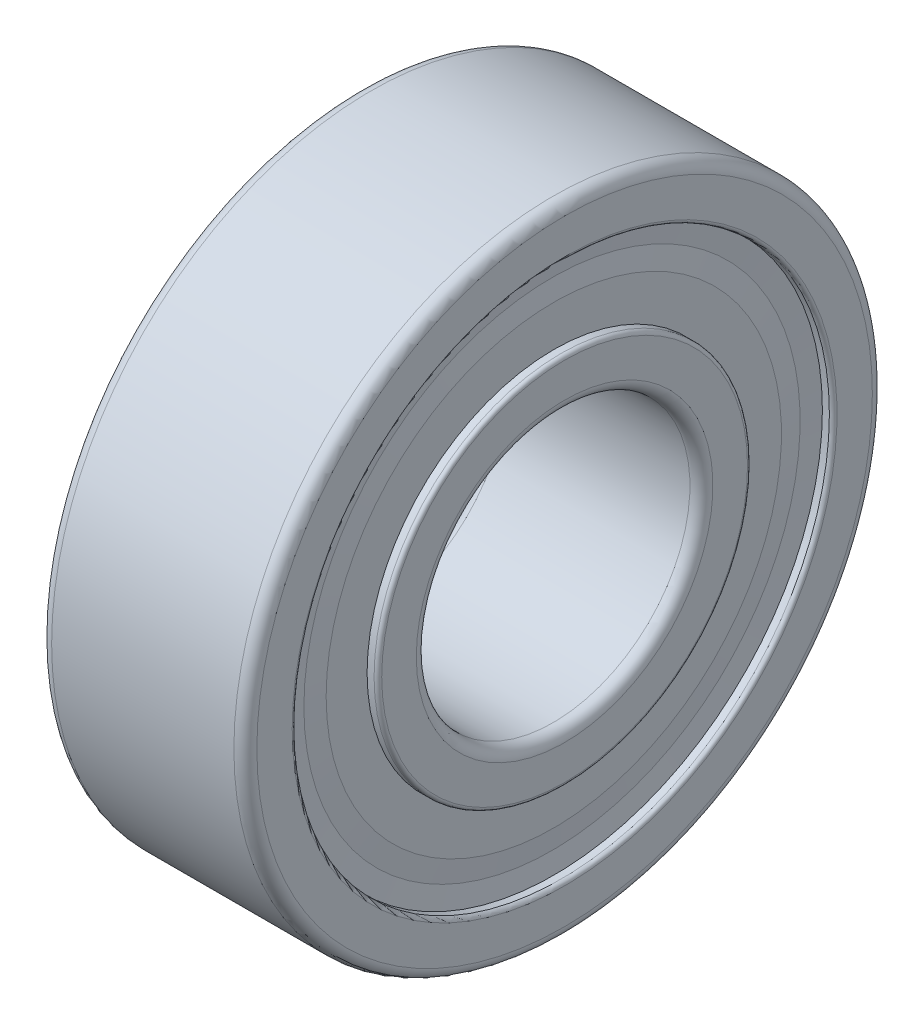
SolidWorks part; units mm, degrees
ref_plane "Front Plane" through (0, 0, 0) normal (0, 0, 1) x (1, 0, 0)
ref_plane "Top Plane" through (0, 0, 0) normal (0, 1, 0) x (1, 0, 0)
ref_plane "Right Plane" through (0, 0, 0) normal (1, 0, 0) x (0, 0, -1)
ref_plane "Plane1" through (0, 0, 0) normal (0, 0, -1) x (-1, 0, 0)
sketch "Sketch1" plane through (0, 0, 0) normal (0, 0, -1) x (-1, 0, 0)
  line L0 (-6.744, 4.763) -> (-0.4, 4.763)
  line L1 (0, 5.163) -> (0, 6.367)
  line L2 (-0.133, 6.5) -> (-0.376, 6.5)
  line L3 (-0.376, 6.5) -> (-0.376, 7.925)
  line L4 (-0.376, 7.925) -> (-0.4387, 8.6375)
  line L5 (-0.4387, 8.6375) -> (-0.376, 9.35)
  line L6 (-0.376, 9.35) -> (-0.133, 9.35)
  line L7 (0, 9.483) -> (0, 10.713)
  line L8 (-0.4, 11.113) -> (-6.744, 11.113)
  line L9 (-7.144, 10.713) -> (-7.144, 9.483)
  line L10 (-7.011, 9.35) -> (-6.768, 9.35)
  line L11 (-6.768, 9.35) -> (-6.7052, 8.6375)
  line L12 (-6.7052, 8.6375) -> (-6.768, 7.925)
  line L13 (-6.768, 7.925) -> (-6.768, 6.5)
  line L14 (-6.768, 6.5) -> (-7.011, 6.5)
  line L15 (-7.144, 6.367) -> (-7.144, 5.163)
  line L16 (-7.1478, 0) -> (0.0038, 0) construction
  arc A0 (-7.144, 5.163) -> (-6.744, 4.763) centre (-6.744, 5.163) ccw
  arc A1 (-0.4, 4.763) -> (0, 5.163) centre (-0.4, 5.163) ccw
  arc A2 (0, 6.367) -> (-0.133, 6.5) centre (-0.133, 6.367) ccw
  arc A3 (-0.133, 9.35) -> (0, 9.483) centre (-0.133, 9.483) ccw
  arc A4 (0, 10.713) -> (-0.4, 11.113) centre (-0.4, 10.713) ccw
  arc A5 (-6.744, 11.113) -> (-7.144, 10.713) centre (-6.744, 10.713) ccw
  arc A6 (-7.144, 9.483) -> (-7.011, 9.35) centre (-7.011, 9.483) ccw
  arc A7 (-7.011, 6.5) -> (-7.144, 6.367) centre (-7.011, 6.367) ccw
revolve "Revolve1" add sketch "Sketch1" angle 360 about L16
